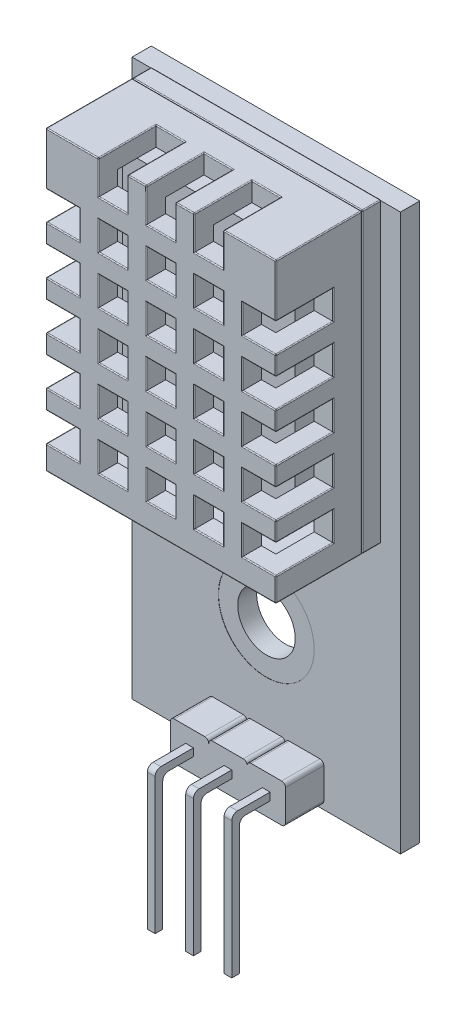
SolidWorks part; units mm, degrees
ref_plane "Front Plane" through (0, 0, 0) normal (0, 0, 1) x (1, 0, 0)
ref_plane "Top Plane" through (0, 0, 0) normal (0, 1, 0) x (1, 0, 0)
ref_plane "Right Plane" through (0, 0, 0) normal (1, 0, 0) x (0, 0, -1)
sketch "Sketch1" plane through (0, 0, 0) normal (0, 0, 1) x (1, 0, 0)
  line L1 (0, 0) -> (12, 0)
  line L2 (0, 0) -> (0, 15.5)
  line L3 (0, 15.5) -> (12, 15.5)
  line L4 (12, 0) -> (12, 15.5)
  dimension "D1" = 12
  dimension "D2" = 15.5
extrude "Boss-Extrude1" add sketch "Sketch1" along normal blind 5.5
shell "Shell2" thickness 1
sketch "Sketch3" plane through (0, 0, 5.5) normal (0, 0, 1) x (1, 0, 0)
  line L0 (12, 15.5) -> (0, 15.5) construction
  line L1 (2.75, 15.5) -> (4.25, 15.5)
  line L2 (2.75, 15.5) -> (2.75, 13.75)
  line L3 (2.75, 13.75) -> (4.25, 13.75)
  line L4 (4.25, 15.5) -> (4.25, 13.75)
  line L5 (5.25, 15.5) -> (6.75, 15.5)
  line L6 (5.25, 15.5) -> (5.25, 13.75)
  line L7 (5.25, 13.75) -> (6.75, 13.75)
  line L8 (6.75, 15.5) -> (6.75, 13.75)
  line L9 (7.75, 15.5) -> (9.25, 15.5)
  line L10 (7.75, 15.5) -> (7.75, 13.75)
  line L11 (7.75, 13.75) -> (9.25, 13.75)
  line L12 (9.25, 15.5) -> (9.25, 13.75)
  line L13 (0, 15.5) -> (0, 0) construction
  dimension "D1" = 1.5
  dimension "D2" = 1.75
  dimension "D4" = 2.75
  dimension "D3" = 3
extrude "Cut-Extrude1" cut sketch "Sketch3" against normal blind 3
sketch "Sketch4" plane through (0, 0, 5.5) normal (0, 0, 1) x (1, 0, 0)
  line L0 (2.75, 13.75) -> (4.25, 13.75) construction
  line L1 (2.75, 12.75) -> (4.25, 12.75)
  line L2 (2.75, 12.75) -> (2.75, 11.25)
  line L3 (2.75, 11.25) -> (4.25, 11.25)
  line L4 (4.25, 12.75) -> (4.25, 11.25)
  line L5 (0, 15.5) -> (0, 0) construction
  line L6 (5.25, 12.75) -> (6.75, 12.75)
  line L7 (5.25, 12.75) -> (5.25, 11.25)
  line L8 (5.25, 11.25) -> (6.75, 11.25)
  line L9 (6.75, 12.75) -> (6.75, 11.25)
  line L10 (7.75, 12.75) -> (9.25, 12.75)
  line L11 (7.75, 12.75) -> (7.75, 11.25)
  line L12 (7.75, 11.25) -> (9.25, 11.25)
  line L13 (9.25, 12.75) -> (9.25, 11.25)
  line L14 (5.25, 10.25) -> (6.75, 10.25)
  line L15 (5.25, 10.25) -> (5.25, 8.75)
  line L16 (5.25, 8.75) -> (6.75, 8.75)
  line L17 (6.75, 10.25) -> (6.75, 8.75)
  line L18 (7.75, 10.25) -> (9.25, 10.25)
  line L19 (7.75, 10.25) -> (7.75, 8.75)
  line L20 (7.75, 8.75) -> (9.25, 8.75)
  line L21 (9.25, 10.25) -> (9.25, 8.75)
  line L22 (5.25, 7.75) -> (6.75, 7.75)
  line L23 (5.25, 7.75) -> (5.25, 6.25)
  line L24 (5.25, 6.25) -> (6.75, 6.25)
  line L25 (6.75, 7.75) -> (6.75, 6.25)
  line L26 (7.75, 7.75) -> (9.25, 7.75)
  line L27 (7.75, 7.75) -> (7.75, 6.25)
  line L28 (7.75, 6.25) -> (9.25, 6.25)
  line L29 (9.25, 7.75) -> (9.25, 6.25)
  line L30 (5.25, 5.25) -> (6.75, 5.25)
  line L31 (5.25, 5.25) -> (5.25, 3.75)
  line L32 (5.25, 3.75) -> (6.75, 3.75)
  line L33 (6.75, 5.25) -> (6.75, 3.75)
  line L34 (7.75, 5.25) -> (9.25, 5.25)
  line L35 (7.75, 5.25) -> (7.75, 3.75)
  line L36 (7.75, 3.75) -> (9.25, 3.75)
  line L37 (9.25, 5.25) -> (9.25, 3.75)
  line L38 (5.25, 2.75) -> (6.75, 2.75)
  line L39 (5.25, 2.75) -> (5.25, 1.25)
  line L40 (5.25, 1.25) -> (6.75, 1.25)
  line L41 (6.75, 2.75) -> (6.75, 1.25)
  line L42 (7.75, 2.75) -> (9.25, 2.75)
  line L43 (7.75, 2.75) -> (7.75, 1.25)
  line L44 (7.75, 1.25) -> (9.25, 1.25)
  line L45 (9.25, 2.75) -> (9.25, 1.25)
  line L46 (2.75, 10.25) -> (4.25, 10.25)
  line L47 (2.75, 10.25) -> (2.75, 8.75)
  line L48 (2.75, 8.75) -> (4.25, 8.75)
  line L49 (4.25, 10.25) -> (4.25, 8.75)
  line L50 (2.75, 7.75) -> (4.25, 7.75)
  line L51 (2.75, 7.75) -> (2.75, 6.25)
  line L52 (2.75, 6.25) -> (4.25, 6.25)
  line L53 (4.25, 7.75) -> (4.25, 6.25)
  line L54 (2.75, 5.25) -> (4.25, 5.25)
  line L55 (2.75, 5.25) -> (2.75, 3.75)
  line L56 (2.75, 3.75) -> (4.25, 3.75)
  line L57 (4.25, 5.25) -> (4.25, 3.75)
  line L58 (2.75, 2.75) -> (4.25, 2.75)
  line L59 (2.75, 2.75) -> (2.75, 1.25)
  line L60 (2.75, 1.25) -> (4.25, 1.25)
  line L61 (4.25, 2.75) -> (4.25, 1.25)
  dimension "D1" = 1.5
  dimension "D2" = 1
  dimension "D3" = 2.75
  dimension "D4" = 3
  dimension "D5" = 5
extrude "Cut-Extrude2" cut sketch "Sketch4" against normal blind 3
sketch "Sketch5" plane through (0, 0, 5.5) normal (0, 0, 1) x (1, 0, 0)
  line L0 (0, 15.5) -> (0, 0) construction
  line L1 (0, 12.75) -> (1.75, 12.75)
  line L2 (0, 12.75) -> (0, 11.25)
  line L3 (0, 11.25) -> (1.75, 11.25)
  line L4 (1.75, 12.75) -> (1.75, 11.25)
  line L7 (2.75, 12.75) -> (2.75, 11.25) construction
  line L8 (10.25, 12.75) -> (12, 12.75)
  line L9 (10.25, 12.75) -> (10.25, 11.25)
  line L10 (10.25, 11.25) -> (12, 11.25)
  line L11 (12, 12.75) -> (12, 11.25)
  line L12 (10.25, 10.25) -> (12, 10.25)
  line L13 (10.25, 10.25) -> (10.25, 8.75)
  line L14 (10.25, 8.75) -> (12, 8.75)
  line L15 (12, 10.25) -> (12, 8.75)
  line L16 (10.25, 7.75) -> (12, 7.75)
  line L17 (10.25, 7.75) -> (10.25, 6.25)
  line L18 (10.25, 6.25) -> (12, 6.25)
  line L19 (12, 7.75) -> (12, 6.25)
  line L20 (10.25, 5.25) -> (12, 5.25)
  line L21 (10.25, 5.25) -> (10.25, 3.75)
  line L22 (10.25, 3.75) -> (12, 3.75)
  line L23 (12, 5.25) -> (12, 3.75)
  line L24 (10.25, 2.75) -> (12, 2.75)
  line L25 (10.25, 2.75) -> (10.25, 1.25)
  line L26 (10.25, 1.25) -> (12, 1.25)
  line L27 (12, 2.75) -> (12, 1.25)
  line L28 (0, 10.25) -> (1.75, 10.25)
  line L29 (0, 10.25) -> (0, 8.75)
  line L30 (0, 8.75) -> (1.75, 8.75)
  line L31 (1.75, 10.25) -> (1.75, 8.75)
  line L32 (0, 7.75) -> (1.75, 7.75)
  line L33 (0, 7.75) -> (0, 6.25)
  line L34 (0, 6.25) -> (1.75, 6.25)
  line L35 (1.75, 7.75) -> (1.75, 6.25)
  line L36 (0, 5.25) -> (1.75, 5.25)
  line L37 (0, 5.25) -> (0, 3.75)
  line L38 (0, 3.75) -> (1.75, 3.75)
  line L39 (1.75, 5.25) -> (1.75, 3.75)
  line L40 (0, 2.75) -> (1.75, 2.75)
  line L41 (0, 2.75) -> (0, 1.25)
  line L42 (0, 1.25) -> (1.75, 1.25)
  line L43 (1.75, 2.75) -> (1.75, 1.25)
  dimension "D1" = 1
  dimension "D2" = 2
  dimension "D3" = 5
extrude "Cut-Extrude3" cut sketch "Sketch5" against normal blind 3
sketch "Sketch6" plane through (0, 0, 0) normal (0, 0, -1) x (-1, 0, 0)
  line L4 (0, 0) -> (0, 15.5)
  line L5 (0, 15.5) -> (-12, 15.5)
  line L6 (-12, 15.5) -> (-12, 0)
  line L7 (-12, 0) -> (0, 0)
  line L8 (0, 0) -> (0, 15.5)
  line L9 (0, 15.5) -> (-12, 15.5)
  line L10 (-12, 15.5) -> (-12, 0)
  line L11 (-12, 0) -> (0, 0)
  line L12 (-1, 14.5) -> (-11, 14.5)
  line L13 (-1, 1) -> (-1, 14.5)
  line L14 (-11, 1) -> (-1, 1)
  line L15 (-11, 14.5) -> (-11, 1)
  line L16 (-1, 14.5) -> (-11, 14.5)
  line L17 (-1, 1) -> (-1, 14.5)
  line L18 (-11, 1) -> (-1, 1)
  line L19 (-11, 14.5) -> (-11, 1)
  dimension "D1" = 0
  dimension "D2" = 0
extrude "Cut-Extrude4" cut sketch "Sketch6" against normal blind 1
ref_plane "Plane1" through (0, 0, 0.99) normal (0, 0, 1) x (1, 0, 0)
sketch "Sketch8" plane through (0, 0, 0.99) normal (0, 0, 1) x (1, 0, 0)
  line L4 (0, 0) -> (12, 0)
  line L5 (0, 15.5) -> (0, 0)
  line L6 (12, 15.5) -> (0, 15.5)
  line L7 (12, 0) -> (12, 15.5)
  line L8 (0, 0) -> (12, 0)
  line L9 (0, 15.5) -> (0, 0)
  line L10 (12, 15.5) -> (0, 15.5)
  line L11 (12, 0) -> (12, 15.5)
  dimension "D1" = 0
extrude "Boss-Extrude3" add sketch "Sketch8" against normal blind 0.99 separate body
fillet "Fillet1" radius 0.05 106 edges at (0, 12.75, 4) (0, 12, 2.5) (0, 11.25, 4) (0, 9.5, 2.5) (0, 8.75, 4) (0, 4.5, 2.5) (0, 2.75, 4) (0, 1.25, 4) (0, 0, 3.25) (0, 7.75, 1) (9.25, 15.5, 4) (8.5, 15.5, 2.5) (7.75, 15.5, 4) (6.75, 15.5, 4) (6, 15.5, 2.5) (3.5, 15.5, 2.5) (2.75, 15.5, 4) (0, 15.5, 3.25) (6, 15.5, 1) (12, 0, 3.25) (12, 2, 2.5) (12, 2.75, 4) (12, 6.25, 4) (12, 7, 2.5) (12, 7.75, 4) (12, 9.5, 2.5) (12, 12, 2.5) (12, 12.75, 4) (12, 15.5, 3.25) (12, 7.75, 1) (0.875, 3.75, 5.5) (1.75, 4.5, 5.5) (0.875, 5.25, 5.5) (0, 5.75, 5.5) (0.875, 6.25, 5.5) (1.75, 7, 5.5) (0.875, 8.75, 5.5) (1.75, 9.5, 5.5) (0.875, 10.25, 5.5) (0.875, 11.25, 5.5) (0, 14.125, 5.5) (3.5, 13.75, 5.5) (4.25, 14.625, 5.5) (4.75, 15.5, 5.5) (5.25, 14.625, 5.5) (6, 13.75, 5.5) (8.5, 13.75, 5.5) (9.25, 14.625, 5.5) (10.625, 15.5, 5.5) (12, 14.125, 5.5) (10.25, 12, 5.5) (11.125, 11.25, 5.5) (11.125, 10.25, 5.5) (11.125, 8.75, 5.5) (12, 8.25, 5.5) (10.25, 7, 5.5) (11.125, 6.25, 5.5) (12, 5.75, 5.5) (11.125, 3.75, 5.5) (12, 3.25, 5.5) (11.125, 2.75, 5.5) (10.25, 2, 5.5) (11.125, 1.25, 5.5) (12, 0.625, 5.5) (6, 0, 5.5) (0, 0.625, 5.5) (0.875, 1.25, 5.5) (1.75, 2, 5.5) (0.875, 2.75, 5.5) (0, 3.25, 5.5) (3.5, 12.75, 5.5) (3.5, 11.25, 5.5) (6.75, 12, 5.5) (6, 12.75, 5.5) (5.25, 12, 5.5) (6, 11.25, 5.5) (9.25, 12, 5.5) (8.5, 12.75, 5.5) (7.75, 12, 5.5) (6.75, 9.5, 5.5) (6, 10.25, 5.5) (5.25, 9.5, 5.5) (8.5, 8.75, 5.5) (6, 7.75, 5.5) (8.5, 7.75, 5.5) (7.75, 7, 5.5) (8.5, 6.25, 5.5) (6, 5.25, 5.5) (5.25, 4.5, 5.5) (6, 3.75, 5.5) (9.25, 4.5, 5.5) (7.75, 4.5, 5.5) (6, 2.75, 5.5) (5.25, 2, 5.5) (9.25, 2, 5.5) (8.5, 2.75, 5.5) (8.5, 1.25, 5.5) (3.5, 10.25, 5.5) (2.75, 9.5, 5.5) (4.25, 7, 5.5) (3.5, 7.75, 5.5) (2.75, 7, 5.5) (4.25, 4.5, 5.5) (2.75, 4.5, 5.5) (3.5, 3.75, 5.5) (2.75, 2, 5.5)
fillet "Fillet2" radius 0.05 12 edges at (6, 15.5, 0.99) (0, 15.5, 0.495) (0, 7.75, 0.99) (0, 0, 0.495) (6, 0, 0.99) (12, 15.5, 0.495) (12, 0, 0.495) (12, 7.75, 0.99) (6, 15.5, 0) (0, 7.75, 0) (6, 0, 0) (12, 7.75, 0)
sketch "Sketch10" plane through (0, 0, 0.99) normal (0, 0, 1) x (1, 0, 0)
  line L14 (1.5, 1.5) -> (10.5, 1.5)
  line L15 (10.5, 1.5) -> (10.5, 14)
  line L16 (10.5, 14) -> (1.5, 14)
  line L17 (1.5, 14) -> (1.5, 1.5)
  line L18 (1.5, 1.5) -> (10.5, 1.5)
  line L19 (10.5, 1.5) -> (10.5, 14)
  line L20 (10.5, 14) -> (1.5, 14)
  line L21 (1.5, 14) -> (1.5, 1.5)
  dimension "D1" = 0.5
extrude "Boss-Extrude4" add sketch "Sketch10" along normal blind 2
sketch "Sketch11" plane through (0, 0, 0) normal (0, 0, -1) x (-1, 0, 0)
  line L0 (-11.95, 0.05) -> (-0.05, 0.05) construction
  line L1 (-13, 15.45) -> (1, 15.45)
  line L2 (-13, 15.45) -> (-13, -13.55)
  line L3 (-13, -13.55) -> (1, -13.55)
  line L4 (1, 15.45) -> (1, -13.55)
  point P4 (-6, 15.45)
  point P7 (-6, 0.05)
  dimension "D1" = 14
  dimension "D2" = 29
  dimension "D3" = 0
  dimension "D4" = 14
extrude "Boss-Extrude5" add sketch "Sketch11" along normal blind 1
sketch "Sketch12" plane through (0, 0, 0) normal (0, 0, 1) x (1, 0, 0)
  line L2 (3, -11.55) -> (3, -13.15)
  line L4 (9, -11.55) -> (9, -13.15)
  line L5 (13, 15.45) -> (13, -13.55) construction
  line L7 (5, -11.55) -> (5, -13.15)
  line L8 (7, -11.55) -> (7, -13.15)
  line L9 (3.2, -11.35) -> (4.8, -11.35)
  line L10 (6.8, -11.35) -> (5.2, -11.35)
  line L11 (8.8, -11.35) -> (7.2, -11.35)
  line L12 (9, -13.35) -> (9, -11.35)
  line L13 (8.8, -13.35) -> (7.2, -13.35)
  line L14 (6.8, -13.35) -> (5.2, -13.35)
  line L15 (4.8, -13.35) -> (3.2, -13.35)
  arc A0 (3, -11.55) -> (3.2, -11.35) centre (3.2, -11.55) cw
  arc A1 (5, -11.55) -> (4.8, -11.35) centre (4.8, -11.55) ccw
  arc A2 (5, -11.55) -> (5.2, -11.35) centre (5.2, -11.55) cw
  arc A3 (3.2, -13.35) -> (3, -13.15) centre (3.2, -13.15) cw
  arc A4 (4.8, -13.35) -> (5, -13.15) centre (4.8, -13.15) ccw
  arc A5 (5, -13.15) -> (5.2, -13.35) centre (5.2, -13.15) ccw
  arc A6 (7, -13.15) -> (6.8, -13.35) centre (6.8, -13.15) cw
  arc A7 (7, -13.15) -> (7.2, -13.35) centre (7.2, -13.15) ccw
  arc A8 (7, -11.55) -> (6.8, -11.35) centre (6.8, -11.55) ccw
  arc A9 (7, -11.55) -> (7.2, -11.35) centre (7.2, -11.55) cw
  arc A10 (9, -11.55) -> (8.8, -11.35) centre (8.8, -11.55) ccw
  arc A11 (9, -13.15) -> (8.8, -13.35) centre (8.8, -13.15) cw
  point P8 (3, -11.35)
  dimension "D3" = 0.2
  dimension "D5" = 0.2
  dimension "D6" = 0.2
  dimension "D8" = 0.2
  dimension "D9" = 0.2
  dimension "D10" = 0.2
  dimension "D11" = 0.2
  dimension "D12" = 0.2
  dimension "D13" = 0.2
  dimension "D14" = 0.2
  dimension "D15" = 0.2
  dimension "D16" = 0.2
  dimension "D1" = 6
  dimension "D2" = 2
  dimension "D4" = 4
  dimension "D7" = 2
extrude "Boss-Extrude6" add sketch "Sketch12" along normal blind 2 contours L15 A4 L7 A1 L9 A0 L2 A3 | L8 A8 L10 A2 L7 A5 L14 A6 | A11 L4 A10 L11 A9 L8 A7 L13
sketch "Sketch13" plane through (0, 0, 2) normal (0, 0, 1) x (1, 0, 0)
  line L0 (3.2, -11.35) -> (4.8, -11.35) construction
  line L1 (3.8, -12.1506) -> (4.2, -12.1506)
  line L2 (3.8, -12.1506) -> (3.8, -12.5494)
  line L3 (3.8, -12.5494) -> (4.2, -12.5494)
  line L4 (4.2, -12.1506) -> (4.2, -12.5494)
  line L5 (3, -11.55) -> (3, -13.15) construction
  line L6 (6.8, -11.35) -> (5.2, -11.35) construction
  line L7 (5.8, -12.1506) -> (6.2, -12.1506)
  line L8 (5.8, -12.1506) -> (5.8, -12.5494)
  line L9 (5.8, -12.5494) -> (6.2, -12.5494)
  line L10 (6.2, -12.1506) -> (6.2, -12.5494)
  line L11 (8.8, -11.35) -> (7.2, -11.35) construction
  line L12 (7.8, -12.1506) -> (8.2, -12.1506)
  line L13 (7.8, -12.1506) -> (7.8, -12.5494)
  line L14 (7.8, -12.5494) -> (8.2, -12.5494)
  line L15 (8.2, -12.1506) -> (8.2, -12.5494)
  point P4 (4, -12.1506)
  point P7 (4, -11.35)
  point P8 (3.8, -12.35)
  point P11 (3, -12.35)
  point P16 (6, -12.1506)
  point P19 (6, -11.35)
  point P24 (8, -12.1506)
  point P27 (8, -11.35)
  dimension "D1" = 0.4
  dimension "D2" = 0.3988
  dimension "D3" = 0
  dimension "D4" = 0
  dimension "D5" = 0.4
  dimension "D6" = 0
  dimension "D7" = 0.4
  dimension "D8" = 0
extrude "Boss-Extrude7" add sketch "Sketch13" along normal blind 2
sketch "Sketch14" plane through (0, -12.5494, 0) normal (0, -1, 0) x (1, 0, 0)
  line L0 (6.2, 4) -> (6.2, 2) construction
  line L1 (5.8, 4) -> (6.2, 4)
  line L2 (5.8, 4) -> (5.8, 3.5997)
  line L3 (5.8, 3.5997) -> (6.2, 3.5997)
  line L4 (6.2, 4) -> (6.2, 3.5997)
  line L5 (4.2, 4) -> (4.2, 2) construction
  line L6 (3.8, 4) -> (4.2, 4)
  line L7 (3.8, 4) -> (3.8, 3.5997)
  line L8 (3.8, 3.5997) -> (4.2, 3.5997)
  line L9 (4.2, 4) -> (4.2, 3.5997)
  line L10 (8.2, 4) -> (8.2, 2) construction
  line L11 (7.8, 4) -> (8.2, 4)
  line L12 (7.8, 4) -> (7.8, 3.5997)
  line L13 (7.8, 3.5997) -> (8.2, 3.5997)
  line L14 (8.2, 4) -> (8.2, 3.5997)
extrude "Boss-Extrude8" add sketch "Sketch14" along normal blind 7
fillet "Fillet3" radius 0.3 1 edges at (4, -12.5494, 3.5997)
fillet "Fillet4" radius 0.3 1 edges at (6, -12.5494, 3.5997)
fillet "Fillet5" radius 0.3 1 edges at (8, -12.5494, 3.5997)
fillet "Fillet6" radius 0.3 1 edges at (4, -12.1506, 4)
fillet "Fillet7" radius 0.3 1 edges at (6, -12.1506, 4)
fillet "Fillet8" radius 0.3 1 edges at (8, -12.1506, 4)
sketch "Sketch15" plane through (0, 0, 0) normal (0, 0, 1) x (1, 0, 0)
  circle A0 centre (6, -6.5668) radius 1.5
  dimension "D1" = 3
extrude "Cut-Extrude5" cut sketch "Sketch15" against normal through all
sketch "Sketch16" plane through (0, 0, 0) normal (0, 0, 1) x (1, 0, 0)
  circle A0 centre (6, -6.5668) radius 2.5
  dimension "D1" = 5
extrude "Cut-Extrude6" cut sketch "Sketch16" against normal blind 0.01
